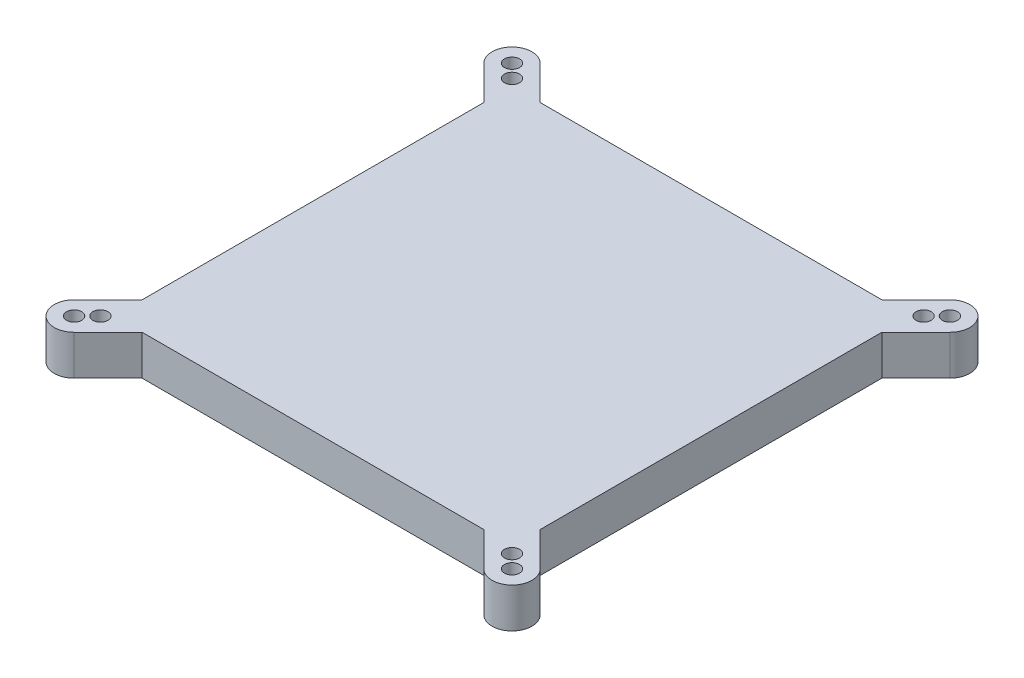
SolidWorks part; units mm, degrees
ref_plane "Front Plane" through (0, 0, 0) normal (0, 0, 1) x (1, 0, 0)
ref_plane "Top Plane" through (0, 0, 0) normal (0, 1, 0) x (1, 0, 0)
ref_plane "Right Plane" through (0, 0, 0) normal (1, 0, 0) x (0, 0, -1)
sketch "Sketch1" plane through (0, 0, 0) normal (0, 1, 0) x (1, 0, 0)
  line L1 (0, 0) -> (200, 0)
  line L2 (0, 0) -> (0, 200)
  line L3 (0, 200) -> (200, 200)
  line L4 (200, 0) -> (200, 200)
  dimension "D1" = 200
  dimension "D2" = 200
extrude "Boss-Extrude1" add sketch "Sketch1" along normal blind 20
sketch "Sketch2" plane through (0, 0, 0) normal (0, -1, 0) x (1, 0, 0)
  line L0 (0, -14.1421) -> (-17.0876, 2.9455)
  line L2 (-2.9455, 17.0876) -> (14.1421, 0)
  line L4 (0, 0) -> (200, -200) construction
  line L5 (200, -200) -> (0, -200) construction
  line L6 (200, 0) -> (200, -200) construction
  line L7 (-10.0166, 10.0166) -> (0, 0) construction
  line L8 (0, -200) -> (200, 0) construction
  line L9 (0, 0) -> (200, 0) construction
  line L10 (0, -200) -> (0, 0) construction
  line L11 (0, -14.1421) -> (0, 0)
  line L12 (0, 0) -> (14.1421, 0)
  line L13 (14.1421, 0) -> (13.2949, 0.1447)
  line L14 (0, -14.1421) -> (-0.1447, -13.2949)
  line L15 (0, 0) -> (0, -14.1421)
  line L16 (14.1421, 0) -> (0, 0)
  line L17 (-17.0876, 2.9455) -> (0, -14.1421)
  line L18 (14.1421, 0) -> (-2.9455, 17.0876)
  arc A0 (-17.0876, 2.9455) -> (-2.9455, 17.0876) centre (-10.0166, 10.0166) cw
  circle A1 centre (-10.0166, 10.0166) radius 3.7971
  circle A2 centre (-3.4154, 3.4154) radius 3.7971
  dimension "D1" = 10
  dimension "D2" = 7.5942
extrude "Boss-Extrude2" add sketch "Sketch2" against normal up to surface (20 mm away)
ref_plane "Plane1" through (0, 0, -100) normal (0, 0, -1) x (-1, 0, 0)
ref_plane "Plane2" through (100, 0, 0) normal (1, 0, 0) x (0, 0, -1)
mirror "Mirror3" about plane through (100, 0, 0) normal (1, 0, 0) of "Boss-Extrude2"
mirror "Mirror4" about plane through (0, 0, -100) normal (0, 0, -1) of "Mirror3", "Boss-Extrude2"
